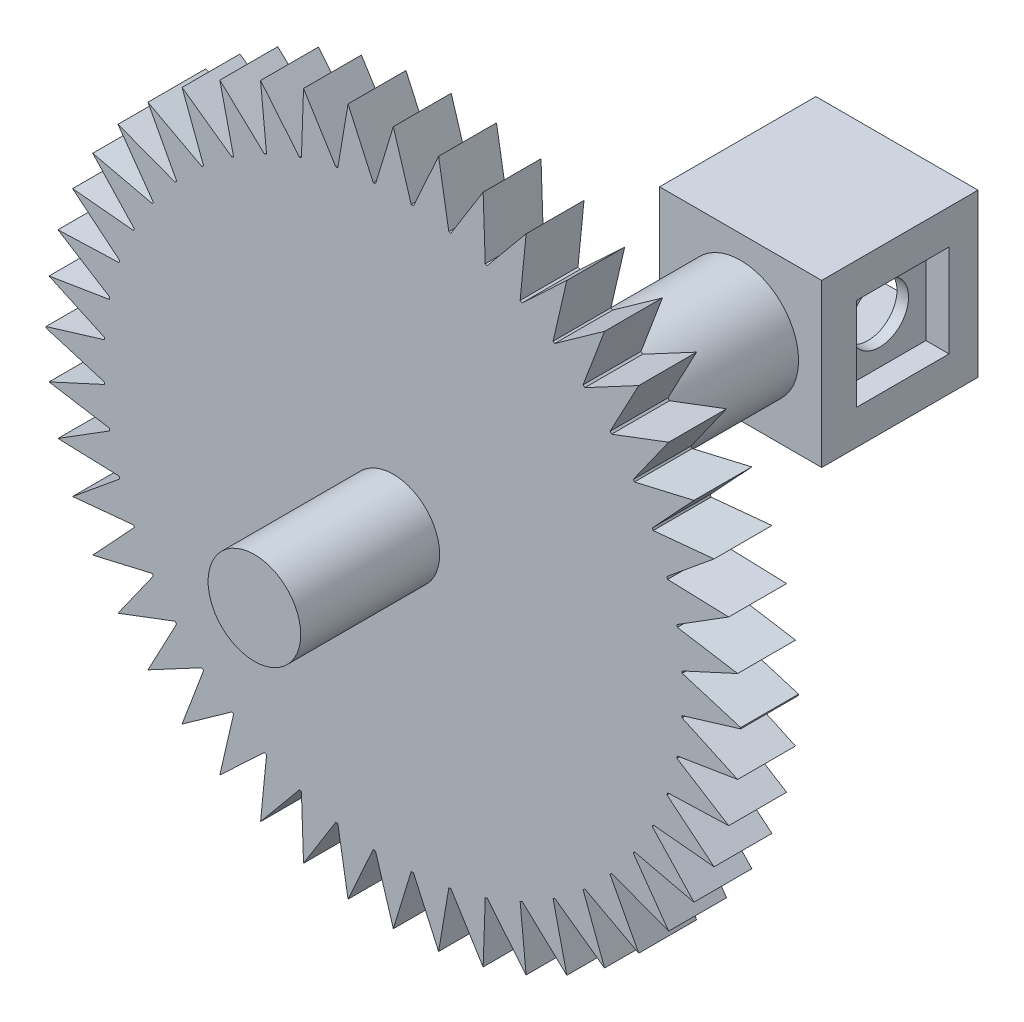
SolidWorks part; units mm, degrees
material "ABS"
ref_plane "Plan de face" through (0, 0, 0) normal (0, 0, 1) x (1, 0, 0)
ref_plane "Plan de dessus" through (0, 0, 0) normal (0, 1, 0) x (1, 0, 0)
ref_plane "Plan de droite" through (0, 0, 0) normal (1, 0, 0) x (0, 0, -1)
sketch "Esquisse1" plane through (0, 0, 0) normal (0, 0, 1) x (1, 0, 0)
  circle A0 centre (0, 0) radius 5
  dimension "D1" = 10
extrude "Boss.-Extru.1" add sketch "Esquisse1" along normal blind 70
sketch "Esquisse2" plane through (0, 0, 70) normal (0, 0, 1) x (1, 0, 0)
  circle A0 centre (0, 0) radius 30
  dimension "D1" = 60
extrude "Boss.-Extru.2" add sketch "Esquisse2" against normal blind 5
sketch "Esquisse3" plane through (0, 0, 0) normal (0, 0, -1) x (-1, 0, 0)
  circle A0 centre (0, 0) radius 3.5
  dimension "D1" = 7
extrude "Boss.-Extru.3" add sketch "Esquisse3" along normal blind 12
sketch "Esquisse4" plane through (0, 0, 70) normal (0, 0, 1) x (1, 0, 0)
  circle A0 centre (0, 0) radius 3.5
  dimension "D1" = 7
extrude "Boss.-Extru.4" add sketch "Esquisse4" along normal blind 12
sketch "Esquisse5" plane through (0, 0, 70) normal (0, 0, 1) x (1, 0, 0)
  line L0 (0, 30) -> (0, -30) construction
  line L1 (-30, 0) -> (30, 0) construction
  line L2 (0, 30) -> (-1.54, 24.9525)
  line L3 (0, 30) -> (1.54, 24.9525)
  line L4 (0, 0) -> (-3.9116, 29.7439) construction
  line L5 (0, 0) -> (-7.7565, 28.9799) construction
  line L6 (0, 0) -> (-11.4689, 27.7212) construction
  line L7 (0, 0) -> (-14.9855, 25.9892) construction
  line L8 (0, 0) -> (-18.2462, 23.8134) construction
  line L9 (0, 0) -> (-21.1954, 21.231) construction
  line L10 (0, 0) -> (-23.7827, 18.2861) construction
  line L11 (0, 0) -> (-25.964, 15.0291) construction
  line L12 (0, 0) -> (-27.7019, 11.5154) construction
  line L13 (0, 0) -> (-28.9669, 7.8051) construction
  line L14 (0, 0) -> (-29.7373, 3.9616) construction
  line L15 (-1.7396, 24.9394) -> (-3.9116, 29.7439)
  line L16 (-3.9116, 29.7439) -> (-4.7931, 24.5362)
  line L17 (-11.4689, 27.7212) -> (-8.104, 23.6501)
  line L18 (-10.9506, 22.4741) -> (-11.4689, 27.7212)
  line L19 (-14.9855, 25.9892) -> (-11.1301, 22.3858)
  line L20 (-14.9855, 25.9892) -> (-13.7983, 20.8472)
  line L21 (-7.7565, 28.9799) -> (-4.9638, 24.5023)
  line L22 (-7.7565, 28.9799) -> (-7.9391, 23.7059)
  line L23 (-21.1954, 21.231) -> (-16.5394, 18.7469)
  line L24 (-21.1954, 21.231) -> (-18.7191, 16.5709)
  line L25 (-18.8511, 16.4206) -> (-23.7827, 18.2861)
  line L26 (-23.7827, 18.2861) -> (-20.7272, 13.9779)
  line L27 (-25.964, 15.0291) -> (-20.8241, 13.8333)
  line L28 (-25.964, 15.0291) -> (-22.367, 11.1676)
  line L29 (-27.7019, 11.5154) -> (-22.4443, 11.0116)
  line L30 (-23.628, 8.1681) -> (-27.7019, 11.5154)
  line L31 (-28.9669, 7.8051) -> (-23.6926, 7.9789)
  line L32 (-28.9669, 7.8051) -> (-24.4939, 5.0049)
  line L33 (-18.2462, 23.8134) -> (-13.9431, 20.7507)
  line L34 (-16.3889, 18.8786) -> (-18.2462, 23.8134)
  line L35 (-30, 0.0504) -> (-24.9499, 1.5819)
  line L36 (-30, 0.0504) -> (-24.9551, -1.4981)
  line L37 (-24.5331, 4.8088) -> (-29.7373, 3.9616)
  line L38 (-29.7373, 3.9616) -> (-24.9383, 1.7556)
  line L39 (30, 0.0504) -> (24.9499, 1.5819)
  line L40 (29.7373, 3.9616) -> (24.9383, 1.7556)
  line L41 (24.5331, 4.8088) -> (29.7373, 3.9616)
  line L42 (28.9669, 7.8051) -> (24.4939, 5.0049)
  line L43 (28.9669, 7.8051) -> (23.6926, 7.9789)
  line L44 (23.628, 8.1681) -> (27.7019, 11.5154)
  line L45 (27.7019, 11.5154) -> (22.4443, 11.0116)
  line L46 (25.964, 15.0291) -> (22.367, 11.1676)
  line L47 (25.964, 15.0291) -> (20.8241, 13.8333)
  line L48 (23.7827, 18.2861) -> (20.7272, 13.9779)
  line L49 (18.8511, 16.4206) -> (23.7827, 18.2861)
  line L50 (21.1954, 21.231) -> (18.7191, 16.5709)
  line L51 (21.1954, 21.231) -> (16.5394, 18.7469)
  line L52 (16.3889, 18.8786) -> (18.2462, 23.8134)
  line L53 (18.2462, 23.8134) -> (13.9431, 20.7507)
  line L54 (14.9855, 25.9892) -> (13.7983, 20.8472)
  line L55 (14.9855, 25.9892) -> (11.1301, 22.3858)
  line L56 (10.9506, 22.4741) -> (11.4689, 27.7212)
  line L57 (11.4689, 27.7212) -> (8.104, 23.6501)
  line L58 (7.7565, 28.9799) -> (7.9391, 23.7059)
  line L59 (7.7565, 28.9799) -> (4.9638, 24.5023)
  line L60 (3.9116, 29.7439) -> (4.7931, 24.5362)
  line L61 (1.7396, 24.9394) -> (3.9116, 29.7439)
  line L62 (0, 30) -> (1.54, 24.9525)
  line L63 (30, -0.0504) -> (24.9499, -1.5819)
  line L64 (29.7373, -3.9616) -> (24.9383, -1.7556)
  line L65 (24.5331, -4.8088) -> (29.7373, -3.9616)
  line L66 (28.9669, -7.8051) -> (24.4939, -5.0049)
  line L67 (28.9669, -7.8051) -> (23.6926, -7.9789)
  line L68 (23.628, -8.1681) -> (27.7019, -11.5154)
  line L69 (27.7019, -11.5154) -> (22.4443, -11.0116)
  line L70 (25.964, -15.0291) -> (22.367, -11.1676)
  line L71 (25.964, -15.0291) -> (20.8241, -13.8333)
  line L72 (23.7827, -18.2861) -> (20.7272, -13.9779)
  line L73 (18.8511, -16.4206) -> (23.7827, -18.2861)
  line L74 (21.1954, -21.231) -> (18.7191, -16.5709)
  line L75 (21.1954, -21.231) -> (16.5394, -18.7469)
  line L76 (16.3889, -18.8786) -> (18.2462, -23.8134)
  line L77 (18.2462, -23.8134) -> (13.9431, -20.7507)
  line L78 (14.9855, -25.9892) -> (13.7983, -20.8472)
  line L79 (14.9855, -25.9892) -> (11.1301, -22.3858)
  line L80 (10.9506, -22.4741) -> (11.4689, -27.7212)
  line L81 (11.4689, -27.7212) -> (8.104, -23.6501)
  line L82 (7.7565, -28.9799) -> (7.9391, -23.7059)
  line L83 (7.7565, -28.9799) -> (4.9638, -24.5023)
  line L84 (3.9116, -29.7439) -> (4.7931, -24.5362)
  line L85 (1.7396, -24.9394) -> (3.9116, -29.7439)
  line L86 (0, -30) -> (1.54, -24.9525)
  line L87 (0, -30) -> (-1.54, -24.9525)
  line L88 (-1.7396, -24.9394) -> (-3.9116, -29.7439)
  line L89 (-3.9116, -29.7439) -> (-4.7931, -24.5362)
  line L90 (-7.7565, -28.9799) -> (-4.9638, -24.5023)
  line L91 (-7.7565, -28.9799) -> (-7.9391, -23.7059)
  line L92 (-11.4689, -27.7212) -> (-8.104, -23.6501)
  line L93 (-10.9506, -22.4741) -> (-11.4689, -27.7212)
  line L94 (-14.9855, -25.9892) -> (-11.1301, -22.3858)
  line L95 (-14.9855, -25.9892) -> (-13.7983, -20.8472)
  line L96 (-18.2462, -23.8134) -> (-13.9431, -20.7507)
  line L97 (-16.3889, -18.8786) -> (-18.2462, -23.8134)
  line L98 (-21.1954, -21.231) -> (-16.5394, -18.7469)
  line L99 (-21.1954, -21.231) -> (-18.7191, -16.5709)
  line L100 (-18.8511, -16.4206) -> (-23.7827, -18.2861)
  line L101 (-23.7827, -18.2861) -> (-20.7272, -13.9779)
  line L102 (-25.964, -15.0291) -> (-20.8241, -13.8333)
  line L103 (-25.964, -15.0291) -> (-22.367, -11.1676)
  line L104 (-27.7019, -11.5154) -> (-22.4443, -11.0116)
  line L105 (-23.628, -8.1681) -> (-27.7019, -11.5154)
  line L106 (-28.9669, -7.8051) -> (-23.6926, -7.9789)
  line L107 (-28.9669, -7.8051) -> (-24.4939, -5.0049)
  line L108 (-24.5331, -4.8088) -> (-29.7373, -3.9616)
  line L109 (-29.7373, -3.9616) -> (-24.9383, -1.7556)
  line L110 (-30, -0.0504) -> (-24.9499, -1.5819)
  circle A0 centre (0, 0) radius 30
  circle A1 centre (0, 0) radius 25
  circle M5 centre (0, 0) radius 30
  dimension "D2" = 50
  dimension "D13" = 3.92
  dimension "D14" = 3.08
  dimension "D15" = 3.08
  dimension "D17" = 0.2
extrude "Enlèv. mat.-Extru.1" cut sketch "Esquisse5" against normal blind 10 contours A1 L2 L15 M5 | A1 L16 L21 M5 | A1 L22 L17 M5 | A1 L18 L19 M5 | A1 L20 L33 M5 | A1 L34 L23 M5 | A1 L24 L25 M5 | A1 L26 L27 M5 | A1 L28 L29 M5 | A1 L30 L31 M5 | A1 L32 L37 M5 | A1 L38 L35 M5 | A1 L110 L109 M5 | A1 L108 L107 M5 | A1 L106 L105 M5 | A1 L104 L103 M5 | A1 L102 L101 M5 | A1 L100 L99 M5 | A1 L98 L97 M5 | A1 L96 L95 M5 | A1 L94 L93 M5 | A1 L92 L91 M5 | A1 L90 L89 M5 | A1 L88 L87 M5 | A1 L61 L3 M5 | A1 L59 L60 M5 | A1 L57 L58 M5 | A1 L55 L56 M5 | A1 L53 L54 M5 | A1 L51 L52 M5 | A1 L49 L50 M5 | A1 L47 L48 M5 | A1 L45 L46 M5 | A1 L43 L44 M5 | A1 L41 L42 M5 | A1 L39 L40 M5 | A1 L64 L63 M5 | A1 L66 L65 M5 | A1 L68 L67 M5 | A1 L70 L69 M5 | A1 L72 L71 M5 | A1 L74 L73 M5 | A1 L76 L75 M5 | A1 L78 L77 M5 | A1 L80 L79 M5 | A1 L82 L81 M5 | A1 L84 L83 M5 | A1 L86 L85 M5 | A0
sketch "Esquisse6" plane through (0, 0, -12) normal (0, 0, -1) x (-1, 0, 0)
  circle A0 centre (0, 0) radius 5
extrude "Enlèv. mat.-Extru.2" cut sketch "Esquisse6" against normal blind 47
sketch "Esquisse7" plane through (0, 0, 82) normal (0, 0, 1) x (1, 0, 0)
  circle A0 centre (0, 0) radius 4
  dimension "D1" = 8
extrude "Boss.-Extru.5" add sketch "Esquisse7" against normal blind 12
sketch "Esquisse8" plane through (0, 0, 35) normal (0, 0, -1) x (-1, 0, 0)
  circle A0 centre (0, 0) radius 5
extrude "Enlèv. mat.-Extru.3" cut sketch "Esquisse8" against normal blind 5
sketch "Esquisse9" plane through (0, 0, 40) normal (0, 0, -1) x (-1, 0, 0)
  line L1 (-7, -7) -> (7, -7)
  line L2 (-7, -7) -> (-7, 7)
  line L3 (-7, 7) -> (7, 7)
  line L4 (7, -7) -> (7, 7)
  line L5 (-7, -7) -> (7, 7) construction
  line L6 (-7, 7) -> (7, -7) construction
  point P0 (0, 0)
  dimension "D1" = 14
  dimension "D2" = 14
extrude "Boss.-Extru.6" add sketch "Esquisse9" along normal blind 13.5
sketch "Esquisse10" plane through (0, 0, 26.5) normal (0, 0, -1) x (-1, 0, 0)
  line L1 (-4, -4) -> (4, -4)
  line L2 (-4, -4) -> (-4, 4)
  line L3 (-4, 4) -> (4, 4)
  line L4 (4, -4) -> (4, 4)
  line L5 (-4, -4) -> (4, 4) construction
  line L6 (-4, 4) -> (4, -4) construction
  point P0 (0, 0)
  dimension "D1" = 8
  dimension "D2" = 8
extrude "Enlèv. mat.-Extru.4" cut sketch "Esquisse10" against normal blind 12
sketch "Esquisse11" plane through (-7, 0, 0) normal (-1, 0, 0) x (0, 0, 1)
  line L0 (26.5, -7) -> (26.5, 7) construction
  line L1 (29, 4) -> (37, 4)
  line L2 (29, 4) -> (29, -4)
  line L3 (29, -4) -> (37, -4)
  line L4 (37, 4) -> (37, -4)
  line L5 (29, 4) -> (37, -4) construction
  line L6 (29, -4) -> (37, 4) construction
  line L7 (26.5, 7) -> (40, 7) construction
  point P0 (33, 0)
  dimension "D1" = 8
  dimension "D2" = 8
  dimension "D3" = 2.5
  dimension "D4" = 3
extrude "Enlèv. mat.-Extru.5" cut sketch "Esquisse11" against normal blind 2
sketch "Esquisse12" plane through (-5, 0, 0) normal (-1, 0, 0) x (0, 0, 1)
  line L0 (29, 4) -> (29, -4) construction
  line L1 (37, 4) -> (29, 4) construction
  circle A0 centre (33, 0) radius 2.5
  dimension "D1" = 5
  dimension "D2" = 4
  dimension "D3" = 4
extrude "Enlèv. mat.-Extru.6" cut sketch "Esquisse12" against normal blind 2
sketch "Esquisse13" plane through (7, 0, 0) normal (1, 0, 0) x (0, 0, -1)
  line L0 (-26.5, 7) -> (-40, 7) construction
  line L1 (-37, 4) -> (-29, 4)
  line L2 (-37, 4) -> (-37, -4)
  line L3 (-37, -4) -> (-29, -4)
  line L4 (-29, 4) -> (-29, -4)
  line L5 (-37, 4) -> (-29, -4) construction
  line L6 (-37, -4) -> (-29, 4) construction
  line L7 (-26.5, 7) -> (-26.5, -7) construction
  point P0 (-33, 0)
  dimension "D1" = 8
  dimension "D2" = 8
  dimension "D3" = 3
  dimension "D4" = 2.5
extrude "Enlèv. mat.-Extru.7" cut sketch "Esquisse13" against normal blind 2
sketch "Esquisse14" plane through (5, 0, 0) normal (1, 0, 0) x (0, 0, -1)
  line L0 (-37, 4) -> (-37, -4) construction
  line L1 (-37, -4) -> (-29, -4) construction
  circle A0 centre (-33, 0) radius 2.5
  dimension "D1" = 5
  dimension "D2" = 4
  dimension "D3" = 4
extrude "Enlèv. mat.-Extru.8" cut sketch "Esquisse14" against normal blind 2
